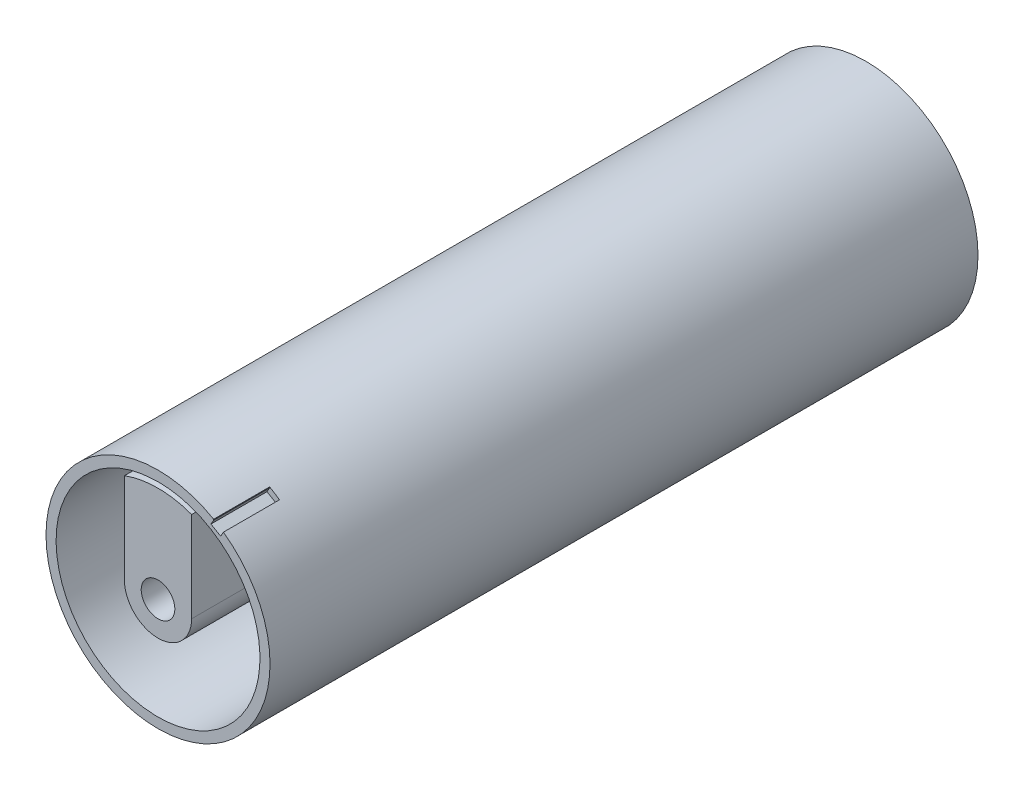
SolidWorks part; units mm, degrees
ref_plane "Спереди" through (0, 0, 0) normal (0, 0, 1) x (1, 0, 0)
ref_plane "Сверху" through (0, 0, 0) normal (0, 1, 0) x (1, 0, 0)
ref_plane "Справа" through (0, 0, 0) normal (1, 0, 0) x (0, 0, -1)
sketch "Эскиз2" plane through (0, 0, 0) normal (0, 0, 1) x (1, 0, 0)
  circle A0 centre (0, 0) radius 20
  circle A1 centre (0, 0) radius 18.2
  dimension "D1" = 40
  dimension "D2" = 36.4
extrude "Бобышка-Вытянуть1" add sketch "Эскиз2" along normal blind 126.4
sketch "Эскиз5" plane through (0, 0, 0) normal (0, 0, -1) x (-1, 0, 0)
  line L0 (0, 0) -> (0, 18.2) construction
  line L1 (0, 0) -> (2.9898, 17.9527) construction
  line L2 (0, 18.2) -> (0, 9.2195)
  line L3 (2.9898, 17.9527) -> (1.5145, 9.0943)
  circle A0 centre (0, 0) radius 18.2 construction
  arc A1 (0, 18.2) -> (2.9898, 17.9527) centre (0, 0) cw
  arc A2 (1.5145, 9.0943) -> (3.3786, 3.6857) centre (7.433, 8.1086) ccw
  circle A3 centre (0, 0) radius 3
  arc A4 (-2.7273, 4.1907) -> (3.3786, 3.6857) centre (0, 0) ccw
  arc A5 (0, 9.2195) -> (-2.7273, 4.1907) centre (-6, 9.2195) cw
  point P16 (0, 5)
  dimension "D2" = 5
  dimension "D3" = 6
  dimension "D4" = 6
  dimension "D1" = 3
extrude "Бобышка-Вытянуть3" add sketch "Эскиз5" against normal through all
sketch "Sketch1" plane through (0, 0, 0) normal (0, 0, -1) x (-1, 0, 0)
  line L0 (0, 18.2) -> (2.9898, 17.9527)
  arc A2 (0, 18.2) -> (2.9898, 17.9527) centre (0, 0) ccw
extrude "Cut-Extrude1" cut sketch "Sketch1" against normal blind 59
sketch "Sketch2" plane through (0, 0, 126.4) normal (0, 0, 1) x (1, 0, 0)
  line L0 (0, 18.2) -> (-2.9898, 17.9527)
  arc A0 (-2.9898, 17.9527) -> (0, 18.2) centre (0, 0) ccw construction
  arc A2 (0, 18.2) -> (-2.9898, 17.9527) centre (0, 0) cw
  dimension "D1" = 18.2
extrude "Cut-Extrude2" cut sketch "Sketch2" against normal blind 59
sketch "Sketch4" plane through (0, 0, 126.4) normal (0, 0, 1) x (1, 0, 0)
  line L0 (0, 0) -> (0, 18.2) construction
  line L1 (0, 18.2) -> (9.1, 15.7617) construction
  line L2 (9.1, 15.7617) -> (0, 0) construction
  line L3 (9.1, 15.7617) -> (9.9499, 17.2337) construction
  line L4 (9.9499, 17.2337) -> (9.4499, 16.3677)
  line L5 (9.4499, 16.3677) -> (11.1819, 15.3677)
  line L6 (11.1819, 15.3677) -> (11.6819, 16.2337)
  circle A0 centre (0, 0) radius 18.2 construction
  circle A2 centre (0, 0) radius 20 construction
  arc A3 (9.9499, 17.2337) -> (11.6819, 16.2337) centre (11.2461, 17.4789) cw
  dimension "D2" = 2
  dimension "D1" = 30
  dimension "D3" = 1
sketch "Sketch3" plane through (0, 0, 126.4) normal (0, 0, 1) x (1, 0, 0)
  line L0 (6, 0) -> (6, 16.1196)
  line L2 (-6, 16.1196) -> (-6, 0)
  circle A0 centre (0, 0) radius 6 construction
  circle A1 centre (0, 0) radius 3
  arc A2 (6, 0) -> (-6, 0) centre (0, 0) cw
  arc A3 (6, 16.1196) -> (-6, 16.1196) centre (0, 0) ccw
  arc A5 (-2.9898, 17.9527) -> (0, 18.2) centre (0, 0) ccw construction
  point P15 (6, 15.8897)
  dimension "D1" = 12
  dimension "D2" = 6
  dimension "D3" = 1
extrude "Boss-Extrude1" add sketch "Sketch3" against normal offset from surface (58.6 mm away) 0.4 separate body up to face at (-0.7283, 8.8066, 67.4)
extrude "Cut-Extrude3" cut sketch "Sketch4" against normal blind 10
